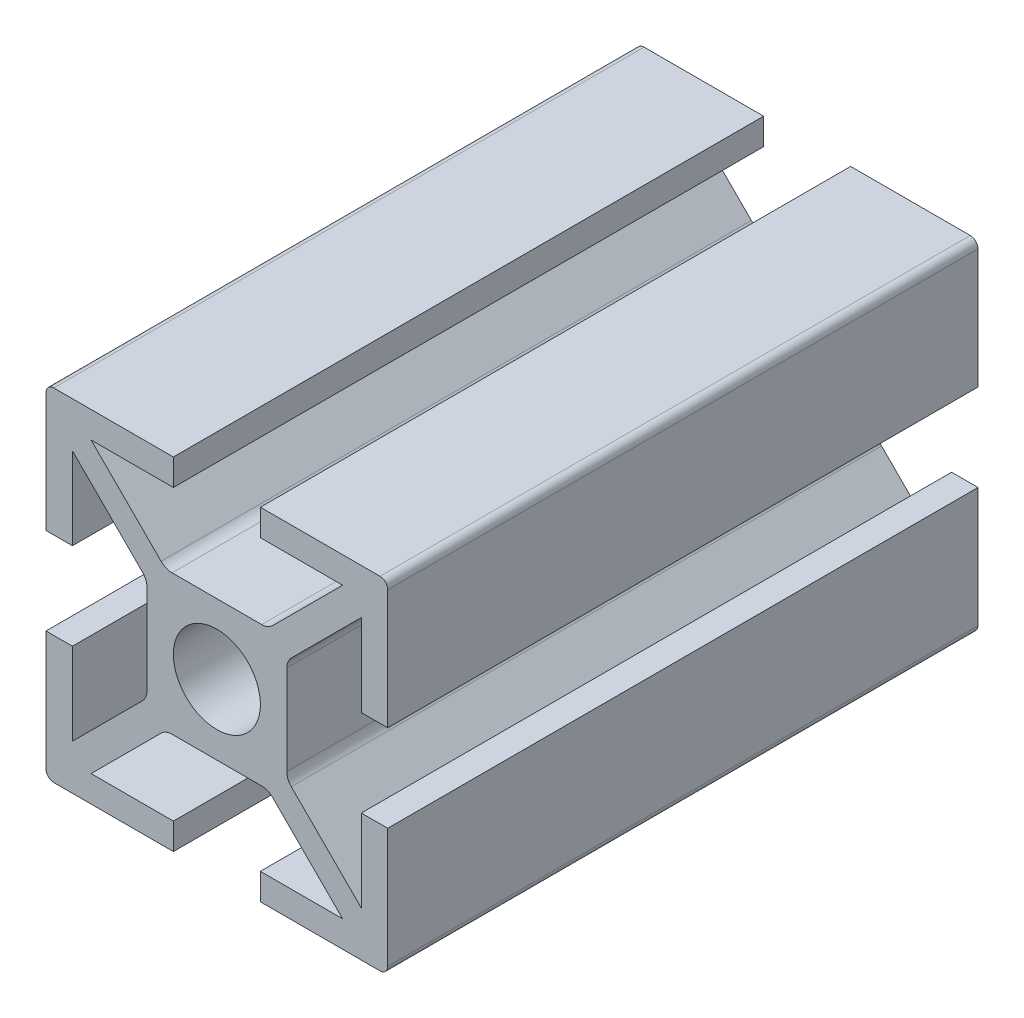
SolidWorks part; units mm, degrees
ref_plane "Plan de face" through (0, 0, 0) normal (0, 0, 1) x (1, 0, 0)
ref_plane "Plan de dessus" through (0, 0, 0) normal (0, 1, 0) x (1, 0, 0)
ref_plane "Plan de droite" through (0, 0, 0) normal (1, 0, 0) x (0, 0, -1)
sketch "Esquisse1" plane through (0, 0, 0) normal (0, 0, 1) x (1, 0, 0)
  line L0 (0, 22) -> (0, -5.6123) construction
  line L1 (-20.8753, 0) -> (5.9514, 0) construction
  line L2 (-2.8, 11) -> (-2.8, 9.3)
  line L3 (-9.3, 2.8) -> (-9.3, 8.0979)
  line L4 (-9.3, 8.0979) -> (-4.5, 3.2979)
  line L5 (-11, 2.8) -> (-11, 11)
  line L6 (-11, 11) -> (-2.8, 11)
  line L7 (-9.3, 2.8) -> (-11, 2.8)
  line L8 (-8.0979, 9.3) -> (-2.8, 9.3)
  line L9 (-8.0979, 9.3) -> (-3.2979, 4.5)
  line L10 (-3.2979, 4.5) -> (3.2979, 4.5)
  line L11 (-4.5, 3.2979) -> (-4.5, -3.2979)
  line L12 (8.0979, 9.3) -> (3.2979, 4.5)
  line L13 (8.0979, 9.3) -> (2.8, 9.3)
  line L14 (2.8, 11) -> (2.8, 9.3)
  line L15 (11, 11) -> (2.8, 11)
  line L16 (11, 2.8) -> (11, 11)
  line L17 (9.3, 2.8) -> (11, 2.8)
  line L18 (9.3, 2.8) -> (9.3, 8.0979)
  line L19 (4.5, 3.2979) -> (4.5, -3.2979)
  line L20 (9.3, 8.0979) -> (4.5, 3.2979)
  line L21 (9.3, -2.8) -> (11, -2.8)
  line L22 (9.3, -8.0979) -> (4.5, -3.2979)
  line L23 (9.3, -2.8) -> (9.3, -8.0979)
  line L24 (11, -2.8) -> (11, -11)
  line L25 (11, -11) -> (2.8, -11)
  line L26 (8.0979, -9.3) -> (3.2979, -4.5)
  line L27 (2.8, -11) -> (2.8, -9.3)
  line L28 (8.0979, -9.3) -> (2.8, -9.3)
  line L29 (-11, -11) -> (-2.8, -11)
  line L30 (-2.8, -11) -> (-2.8, -9.3)
  line L31 (-8.0979, -9.3) -> (-2.8, -9.3)
  line L32 (-3.2979, -4.5) -> (3.2979, -4.5)
  line L33 (-8.0979, -9.3) -> (-3.2979, -4.5)
  line L34 (-9.3, -8.0979) -> (-4.5, -3.2979)
  line L35 (-9.3, -2.8) -> (-9.3, -8.0979)
  line L36 (-9.3, -2.8) -> (-11, -2.8)
  line L37 (-11, -2.8) -> (-11, -11)
  point P17 (0, 4.5)
  point P27 (4.5, 0)
  point P41 (-4.5, 0)
  dimension "D1" = 11
  dimension "D2" = 11
  dimension "D3" = 2.8
  dimension "D4" = 2.8
  dimension "D5" = 1.7
  dimension "D6" = 1.7
  dimension "D7" = 1.7
  dimension "D8" = 1.7
  dimension "D9" = 4.8
  dimension "D10" = 4.8
extrude "Extrusion1" add sketch "Esquisse1" along normal blind 38
sketch "Esquisse2" plane through (0, 0, 0) normal (0, 0, -1) x (-1, 0, 0)
  circle A0 centre (0, 0) radius 2.8
  dimension "D1" = 5.6
extrude "Enlèv. mat.-Extru.1" cut sketch "Esquisse2" against normal through all
fillet "Congé1" radius 0.5 4 edges at (11, -11, 19) (-11, -11, 19) (-11, 11, 19) (11, 11, 19)
fillet "Congé2" radius 1 8 edges at (-4.5, -3.2979, 19) (-4.5, 3.2979, 19) (3.2979, -4.5, 19) (-3.2979, -4.5, 19) (4.5, -3.2979, 19) (4.5, 3.2979, 19) (-3.2979, 4.5, 19) (3.2979, 4.5, 19)
